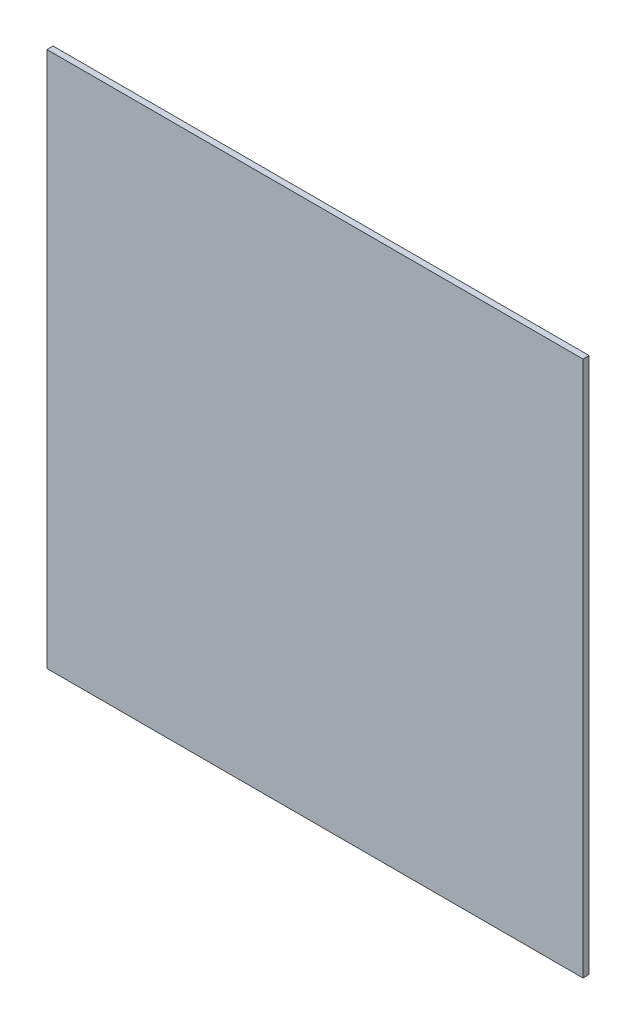
SolidWorks part; units mm, degrees
ref_plane "Plan de face" through (0, 0, 0) normal (0, 0, 1) x (1, 0, 0)
ref_plane "Plan de dessus" through (0, 0, 0) normal (0, 1, 0) x (1, 0, 0)
ref_plane "Plan de droite" through (0, 0, 0) normal (1, 0, 0) x (0, 0, -1)
sketch "Esquisse1" plane through (0, 0, 0) normal (0, 0, 1) x (1, 0, 0)
  line L1 (0, 0) -> (220, 0)
  line L2 (0, 0) -> (0, 220)
  line L3 (0, 220) -> (220, 220)
  line L4 (220, 0) -> (220, 220)
  dimension "D1" = 220
  dimension "D2" = 220
extrude "Boss.-Extru.1" add sketch "Esquisse1" along normal blind 2.5
